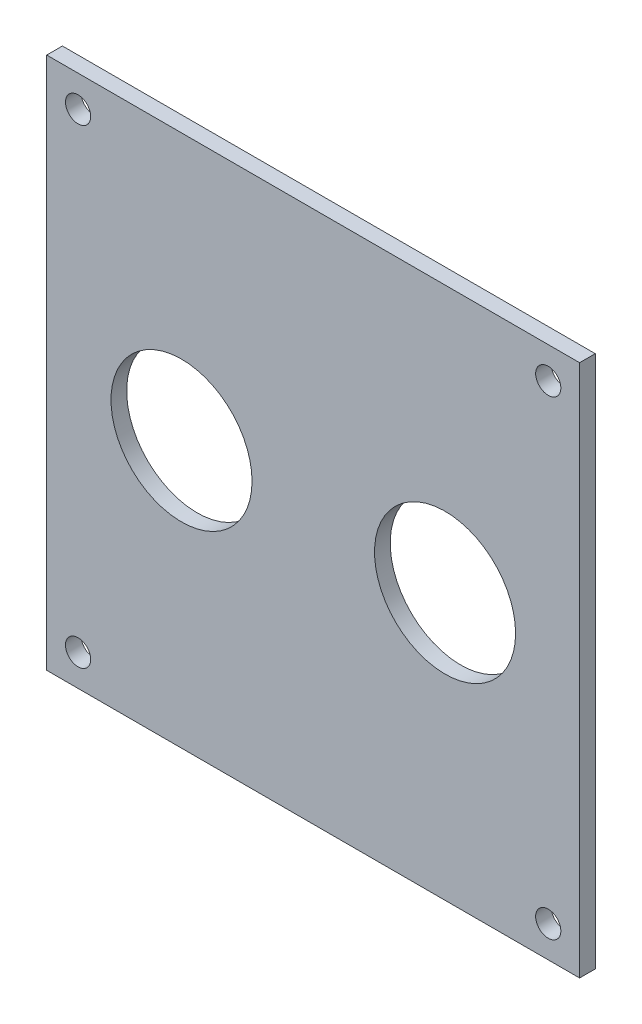
SolidWorks part; units mm, degrees
ref_plane "Front Plane" through (0, 0, 0) normal (0, 0, 1) x (1, 0, 0)
ref_plane "Top Plane" through (0, 0, 0) normal (0, 1, 0) x (1, 0, 0)
ref_plane "Right Plane" through (0, 0, 0) normal (1, 0, 0) x (0, 0, -1)
sketch "Sketch1" plane through (0, 0, 0) normal (0, 0, 1) x (1, 0, 0)
  line L1 (0, 0) -> (107.95, 0)
  line L2 (0, 0) -> (0, 107.95)
  line L3 (0, 107.95) -> (107.95, 107.95)
  line L4 (107.95, 0) -> (107.95, 107.95)
  dimension "D1" = 107.95
extrude "Boss-Extrude1" add sketch "Sketch1" along normal blind 3.175
sketch "Sketch2" plane through (0, 0, 0) normal (0, 0, -1) x (-1, 0, 0)
  line L0 (0, 107.95) -> (0, 0) construction
  line L1 (0, 0) -> (-107.95, 0) construction
  line L2 (-107.95, 0) -> (-107.95, 107.95) construction
  line L3 (-107.95, 107.95) -> (0, 107.95) construction
  circle A0 centre (-6.35, 101.6) radius 2.5527
  circle A1 centre (-101.6, 101.6) radius 2.5527
  circle A2 centre (-101.6, 6.35) radius 2.5527
  circle A3 centre (-6.35, 6.35) radius 2.5527
  dimension "D1" = 5.1054
  dimension "D2" = 5.1054
  dimension "D3" = 5.1054
  dimension "D4" = 5.1054
  dimension "D5" = 6.35
  dimension "D6" = 6.35
  dimension "D7" = 6.35
  dimension "D8" = 6.35
  dimension "D9" = 6.35
  dimension "D10" = 6.35
  dimension "D11" = 6.35
  dimension "D12" = 6.35
extrude "Cut-Extrude1" cut sketch "Sketch2" against normal blind 3.175
sketch "Sketch3" plane through (0, 0, 3.175) normal (0, 0, 1) x (1, 0, 0)
  line L3 (0, 107.95) -> (0, 0) construction
  line L4 (107.95, 107.95) -> (0, 107.95) construction
  circle A0 centre (27.305, 53.975) radius 14.2875
  circle A1 centre (80.6958, 53.975) radius 14.2875
  point P4 (0, 53.975)
  dimension "D1" = 28.575
  dimension "D2" = 53.3908
  dimension "D3" = 27.305
  dimension "D4" = 53.975
extrude "Cut-Extrude2" cut sketch "Sketch3" against normal blind 3.175
